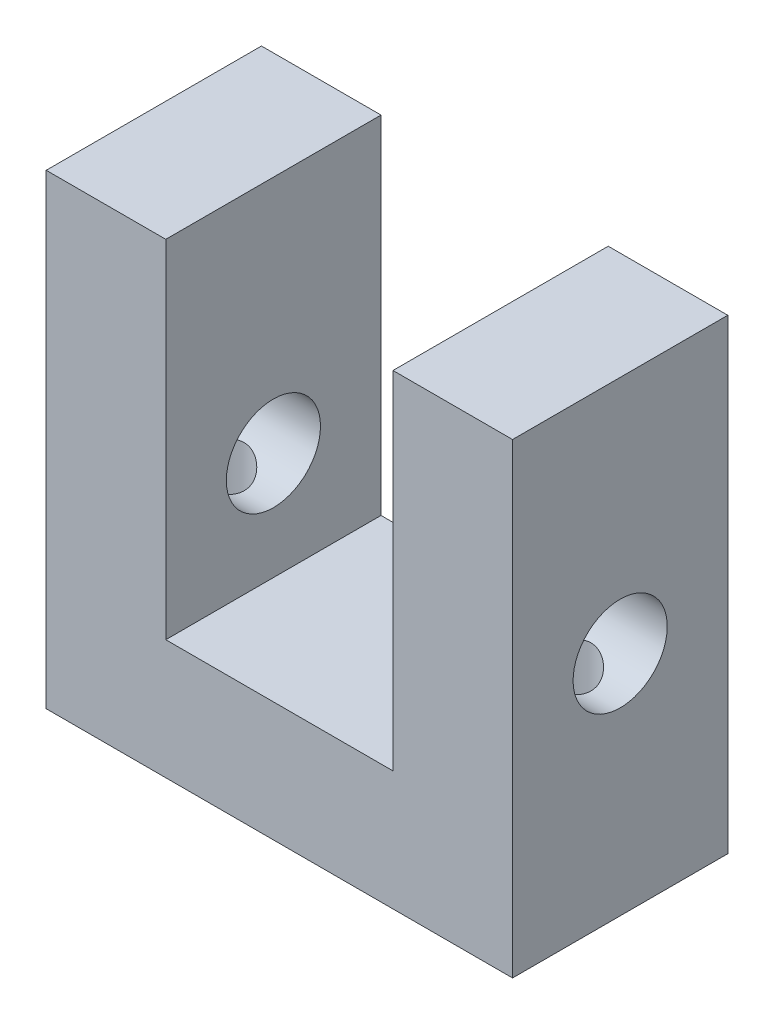
SolidWorks part; units mm, degrees
ref_plane "Front Plane" through (0, 0, 0) normal (0, 0, 1) x (1, 0, 0)
ref_plane "Top Plane" through (0, 0, 0) normal (0, 1, 0) x (1, 0, 0)
ref_plane "Right Plane" through (0, 0, 0) normal (1, 0, 0) x (0, 0, -1)
sketch "Sketch1" plane through (0, 0, 0) normal (0, 0, 1) x (1, 0, 0)
  line L0 (-19.5, 0) -> (19.5, 0)
  line L1 (19.5, 0) -> (19.5, 39)
  line L2 (19.5, 39) -> (9.5, 39)
  line L3 (9.5, 39) -> (9.5, 10)
  line L4 (9.5, 10) -> (-9.5, 10)
  line L5 (-9.5, 10) -> (-9.5, 39)
  line L6 (-9.5, 39) -> (-19.5, 39)
  line L7 (-19.5, 39) -> (-19.5, 0)
  line L8 (0, 0) -> (0, 14.3367) construction
  dimension "D1" = 10
  dimension "D2" = 10
  dimension "D3" = 39
  dimension "D4" = 39
extrude "Boss-Extrude1" add sketch "Sketch1" along normal blind 18
sketch "Sketch3" plane through (19.5, 0, 0) normal (1, 0, 0) x (0, 0, -1)
  line L0 (-9, 39) -> (-9, 19) construction
  line L1 (-18, 39) -> (0, 39) construction
  circle A0 centre (-9, 19) radius 3.937
  dimension "D1" = 7.874
  dimension "D2" = 20
extrude "Cut-Extrude1" cut sketch "Sketch3" against normal through all
hole_wizard "1/4-20 Tapped Hole1" positions "Sketch4" profile "Sketch6" tap size "1/4-20" standard "ANSI Inch"
sketch "Sketch4" plane through (0, 0, 0) normal (0, -1, 0) x (-1, 0, 0)
  line L0 (19.5, -9) -> (-19.5, -9) construction
  line L1 (19.5, -18) -> (19.5, 0) construction
  line L2 (-19.5, -18) -> (-19.5, 0) construction
  line L5 (0, 0) -> (0, -9) construction
  line L6 (14.5, -18) -> (14.5, -9) construction
  line L9 (9.5, -18) -> (19.5, -18) construction
  point P17 (14.5, -9)
  point P19 (-14.5, -9)
  point P30 (0, 0)
cosmetic thread "Hole Thread1" parameters "D1"=3.048, "D2"=6.35
cosmetic thread "Hole Thread2" parameters "D1"=3.048, "D2"=6.35
sketch "Sketch6" plane through (14.5, 0, 9) normal (1, 0, 0) x (0, 0, -1)
  line L0 (0, 0) -> (0, 20.5838)
  line L1 (0, 20.5838) -> (2.5527, 19.05)
  line L2 (2.5527, 19.05) -> (2.5527, 0)
  line L5 (2.5527, 0) -> (0, 0)
  line L10 (0, 20.5838) -> (-2.5527, 19.05) construction
  line L11 (0, -6.35) -> (0, 107.95) construction
  dimension "Tap Drill Dia." = 5.1054
  dimension "Tap Drill Depth" = 19.05
  dimension "Drill Angle" = 118
